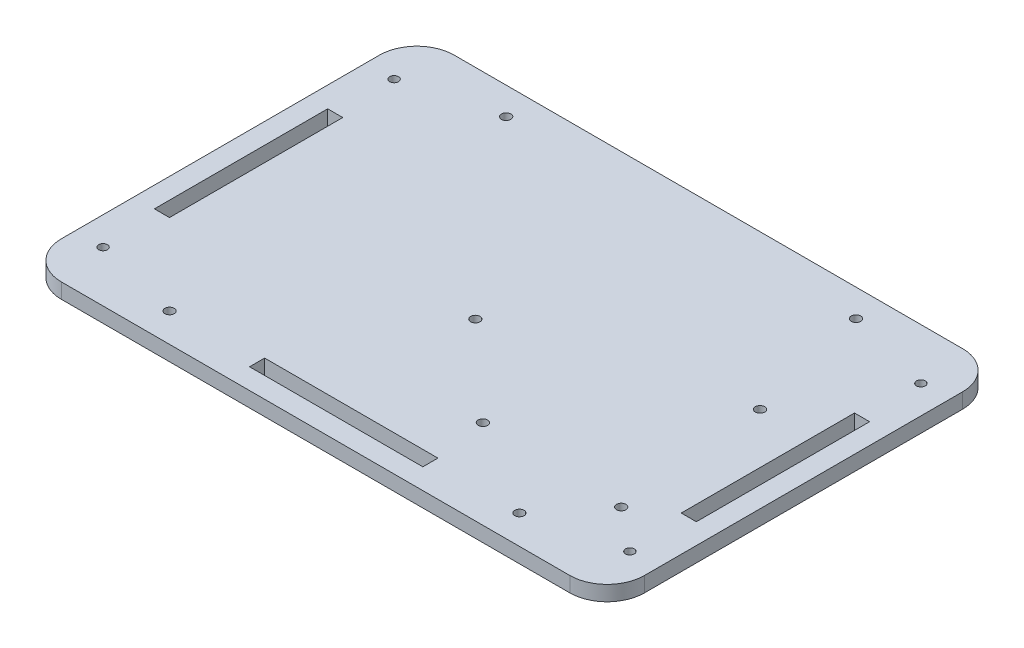
SolidWorks part; units mm, degrees
ref_plane "Front Plane" through (0, 0, 0) normal (0, 0, 1) x (1, 0, 0)
ref_plane "Top Plane" through (0, 0, 0) normal (0, 1, 0) x (1, 0, 0)
ref_plane "Right Plane" through (0, 0, 0) normal (1, 0, 0) x (0, 0, -1)
sketch "Sketch1" plane through (0, 0, 0) normal (0, 1, 0) x (1, 0, 0)
  line L1 (-55.2072, 101.2499) -> (117.5428, 101.2499)
  line L2 (-67.9072, 88.5499) -> (-67.9072, -19.5301)
  line L3 (-55.2072, -32.2301) -> (117.5428, -32.2301)
  line L4 (130.2428, 88.5499) -> (130.2428, -19.5301)
  arc A0 (-55.2072, 101.2499) -> (-67.9072, 88.5499) centre (-55.2072, 88.5499) ccw
  arc A1 (-67.9072, -19.5301) -> (-55.2072, -32.2301) centre (-55.2072, -19.5301) ccw
  arc A2 (117.5428, -32.2301) -> (130.2428, -19.5301) centre (117.5428, -19.5301) ccw
  arc A3 (117.5428, 101.2499) -> (130.2428, 88.5499) centre (117.5428, 88.5499) cw
  point P6 (-67.9072, 101.2499)
  point P9 (-67.9072, -32.2301)
  point P12 (130.2428, -32.2301)
  dimension "D3" = 12.7
  dimension "D1" = 133.48
  dimension "D2" = 198.15
extrude "Main" add sketch "Sketch1" along normal blind 5.13
sketch "Sketch2" plane through (0, 5.13, 0) normal (0, 1, 0) x (1, 0, 0)
  line L0 (117.5428, 101.2499) -> (-55.2072, 101.2499) construction
  line L1 (-60.9072, 63.9499) -> (-55.7772, 63.9499)
  line L2 (-60.9072, 63.9499) -> (-60.9072, 5.0699)
  line L3 (-60.9072, 5.0699) -> (-55.7772, 5.0699)
  line L4 (-55.7772, 63.9499) -> (-55.7772, 5.0699)
  line L5 (31.1678, 101.2499) -> (31.1678, -32.2301) construction
  line L6 (-55.2072, -32.2301) -> (117.5428, -32.2301) construction
  line L7 (130.2428, 34.5099) -> (-67.9072, 34.5099) construction
  line L8 (130.2428, -19.5301) -> (130.2428, 88.5499) construction
  line L13 (123.2428, 63.9499) -> (118.1128, 63.9499)
  line L14 (123.2428, 63.9499) -> (123.2428, 5.0699)
  line L15 (118.1128, 63.9499) -> (118.1128, 5.0699)
  line L16 (123.2428, 5.0699) -> (118.1128, 5.0699)
  line L17 (-67.9072, 88.5499) -> (-67.9072, -19.5301) construction
  circle A2 centre (-58.3472, -14.9301) radius 1.5
  circle A3 centre (-58.3472, 83.9499) radius 1.5
  circle A4 centre (120.6828, 83.9499) radius 1.5
  circle A5 centre (120.6828, -14.9301) radius 1.5
  dimension "D15" = 3
  dimension "D16" = 3
  dimension "D2" = 5.13
  dimension "D3" = 7
  dimension "D5" = 37.3
  dimension "D7" = 58.88
  dimension "D10" = 20
  dimension "D11" = 20
  dimension "D17" = 9.56
  dimension "D18" = 9.56
extrude "Cut-Extrude1" cut sketch "Sketch2" against normal blind 5.13
sketch "Sketch3" plane through (0, 5.13, 0) normal (0, 1, 0) x (1, 0, 0)
  line L0 (1.7278, -20.1001) -> (1.7278, -25.2301)
  line L1 (1.7278, -20.1001) -> (60.6078, -20.1001)
  line L2 (1.7278, -25.2301) -> (60.6078, -25.2301)
  line L3 (60.6078, -20.1001) -> (60.6078, -25.2301)
  line L4 (-55.2072, -32.2301) -> (117.5428, -32.2301) construction
  line L6 (-67.9072, 88.5499) -> (-67.9072, -19.5301) construction
  dimension "D1" = 58.88
  dimension "D2" = 7
  dimension "D3" = 69.635
  dimension "D4" = 5.13
extrude "tooth slot" cut sketch "Sketch3" against normal up to next
sketch "Rubber feet sketch" plane through (0, 5.13, 0) normal (0, 1, 0) x (-1, 0, 0)
  circle A0 centre (43.8217, -81.9441) radius 4.6674
  circle A1 centre (-106.1783, -81.9441) radius 4.6674
  circle A2 centre (43.8217, 13.0559) radius 4.6674
  circle A3 centre (-106.1783, 13.0559) radius 4.6674
hole_wizard "M3 Clearance Hole1" positions "Sketch5" profile "Sketch4" hole size "M3" standard "Ansi Metric"
sketch "Sketch5" plane through (0, 5.13, 0) normal (0, 1, 0) x (-1, 0, 0)
  line L1 (67.9072, -88.5499) -> (67.9072, 19.5301) construction
  point P0 (28.2722, 22.4013)
  dimension "D1" = 39.635
sketch "Sketch4" plane through (-28.2722, 5.13, 22.4013) normal (1, 0, 0) x (0, 0, 1)
  line L0 (0, 0) -> (0, 6.0614)
  line L1 (0, 6.0614) -> (1.6, 5.1)
  line L2 (1.6, 5.1) -> (1.6, 0)
  line L5 (1.6, 0) -> (0, 0)
  line L10 (0, 6.0614) -> (-1.6, 5.1) construction
  line L11 (0, -6.35) -> (0, 107.95) construction
  dimension "Hole Dia." = 3.2
  dimension "Hole Depth" = 5.1
  dimension "Drill Angle" = 118
pattern_linear "LPattern1" count 2 spacing 118.88 along (1, 0, 0) count 2 spacing 114.36 along (0, 0, -1) of "M3 Clearance Hole1"
hole_wizard "M3 Clearance Hole4" positions "Sketch11" profile "Sketch10" hole size "M3" standard "Ansi Metric"
sketch "Sketch11" plane through (0, 5.13, 0) normal (0, 1, 0) x (-1, 0, 0)
  point P2 (-100.9988, -48.96)
  point P3 (-106.1465, 3.364)
  point P4 (-57.8188, 2.04)
  point P5 (-26.0688, -27.17)
  dimension "D1" = 29.21
  dimension "D2" = 31.75
sketch "Sketch10" plane through (100.9988, 5.13, -48.96) normal (1, 0, 0) x (0, 0, 1)
  line L0 (0, 0) -> (0, 6.0614)
  line L1 (0, 6.0614) -> (1.6, 5.1)
  line L2 (1.6, 5.1) -> (1.6, 0)
  line L5 (1.6, 0) -> (0, 0)
  line L10 (0, 6.0614) -> (-1.6, 5.1) construction
  line L11 (0, -6.35) -> (0, 107.95) construction
  dimension "Hole Dia." = 3.2
  dimension "Hole Depth" = 5.1
  dimension "Drill Angle" = 118
